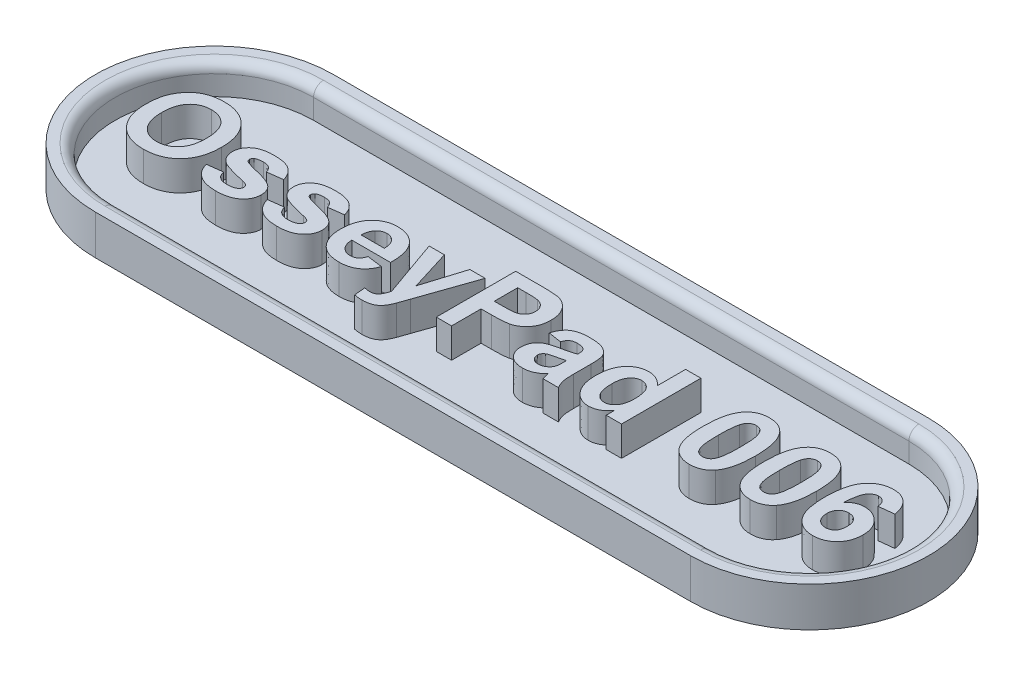
SolidWorks part; units mm, degrees
ref_plane "Front Plane" through (0, 0, 0) normal (0, 0, 1) x (1, 0, 0)
ref_plane "Top Plane" through (0, 0, 0) normal (0, 1, 0) x (1, 0, 0)
ref_plane "Right Plane" through (0, 0, 0) normal (1, 0, 0) x (0, 0, -1)
sketch "Sketch1" plane through (0, 0, 0) normal (0, 1, 0) x (1, 0, 0)
  line L0 (-15, 0) -> (15, 0) construction
  line L1 (-15, 6) -> (15, 6)
  line L2 (-15, -6) -> (15, -6)
  arc A0 (-15, 6) -> (-15, -6) centre (-15, 0) ccw
  arc A1 (15, -6) -> (15, 6) centre (15, 0) ccw
  point P2 (0, 0)
  dimension "D1" = 12
  dimension "D2" = 30
extrude "Boss-Extrude1" add sketch "Sketch1" along normal blind 2
sketch "Sketch2" plane through (0, 2, 0) normal (0, 1, 0) x (1, 0, 0)
  line L0 (-15, 0) -> (15, 0) construction
  line L1 (-15, 5) -> (15, 5)
  line L2 (-15, -5) -> (15, -5)
  arc A0 (-15, 5) -> (-15, -5) centre (-15, 0) ccw
  arc A1 (15, -5) -> (15, 5) centre (15, 0) ccw
  point P2 (0, 0)
  dimension "D1" = 30
  dimension "D2" = 10
extrude "Cut-Extrude1" cut sketch "Sketch2" against normal blind 1.5
sketch "Sketch3" plane through (0, 0.5, 0) normal (0, 1, 0) x (1, 0, 0)
  line L0 (-21, -1.995) -> (21, -1.995) construction
  line L1 (0, -8.7006) -> (0, 6.9821) construction
  line L3 (-15, -5) -> (15, -5) construction
  text T0 "OsseyPad 006" font "Arial" height 4
  dimension "D1" = 3.005
extrude "Boss-Extrude2" add sketch "Sketch3" along normal blind 1.5
fillet "Fillet1" radius 0.5 4 edges at (0, 2, -5) (20, 2, 0) (0, 2, 5) (-20, 2, 0)
